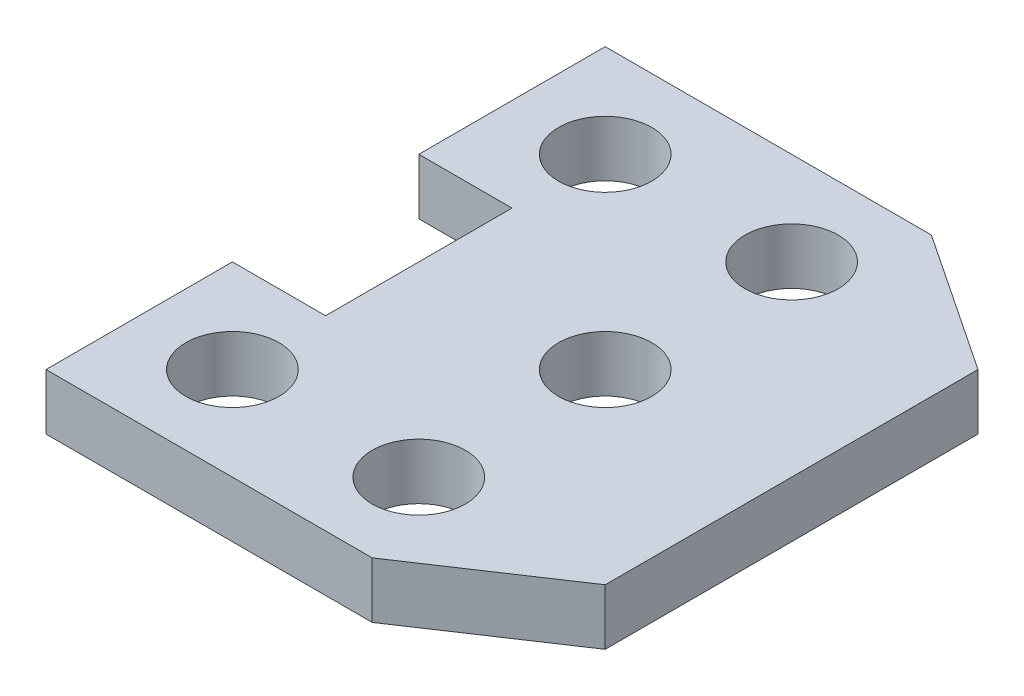
SolidWorks part; units mm, degrees
ref_plane "Front Plane" through (0, 0, 0) normal (0, 0, 1) x (1, 0, 0)
ref_plane "Top Plane" through (0, 0, 0) normal (0, 1, 0) x (1, 0, 0)
ref_plane "Right Plane" through (0, 0, 0) normal (1, 0, 0) x (0, 0, -1)
sketch "Sketch2" plane through (0, 0, 0) normal (0, 1, 0) x (1, 0, 0)
  line L0 (0, 0) -> (70, 0)
  line L1 (70, 0) -> (100, 20)
  line L2 (100, 20) -> (100, 100)
  line L3 (100, 100) -> (70, 120)
  line L4 (70, 120) -> (0, 120)
  line L5 (0, 120) -> (0, 80)
  line L6 (0, 80) -> (20, 80)
  line L7 (20, 80) -> (20, 40)
  line L8 (20, 40) -> (0, 40)
  line L9 (0, 40) -> (0, 0)
  circle A0 centre (20, 100) radius 10
  circle A1 centre (60, 100) radius 10
  circle A2 centre (60, 20) radius 10
  circle A3 centre (20, 20) radius 10
  circle A4 centre (60, 60) radius 10
  point P21 (0, 0)
  point P22 (0, 0)
  point P23 (100, 60)
  dimension "D7" = 20
  dimension "D9" = 20
  dimension "D10" = 20
  dimension "D11" = 20
  dimension "D12" = 40
  dimension "D16" = 20
  dimension "D1" = 20
  dimension "D2" = 20
  dimension "D3" = 40
  dimension "D4" = 40
  dimension "D5" = 70
  dimension "D6" = 100
  dimension "D8" = 40
  dimension "D13" = 40
  dimension "D14" = 40
  dimension "D15" = 20
  dimension "D17" = 40
  dimension "D18" = 20
  dimension "D19" = 20
  dimension "D20" = 70
other "AlignGroup1"
extrude "Boss-Extrude1" add sketch "Sketch2" along normal blind 12
